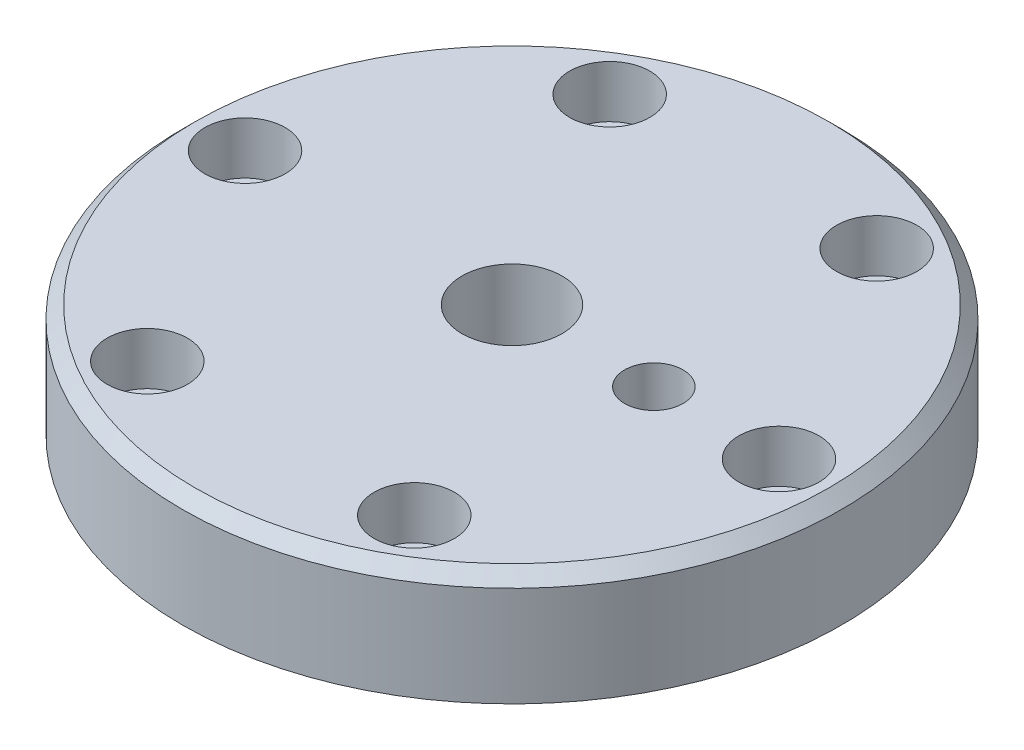
SolidWorks part; units mm, degrees
ref_plane "Front Plane" through (0, 0, 0) normal (0, 0, 1) x (1, 0, 0)
ref_plane "Top Plane" through (0, 0, 0) normal (0, 1, 0) x (1, 0, 0)
ref_plane "Right Plane" through (0, 0, 0) normal (1, 0, 0) x (0, 0, -1)
sketch "Sketch1" plane through (0, 0, 0) normal (0, 1, 0) x (1, 0, 0)
  circle A0 centre (0, 0) radius 79
  circle A1 centre (0, 0) radius 12
extrude "Boss-Extrude1" add sketch "Sketch1" along normal blind 27
hole_wizard "CBORE for M5 Hex Head Bolt1" positions "Sketch2" profile "Sketch3" counterbore size "M5" standard "ANSI Metric" end condition through all
sketch "Sketch2" plane through (0, 27, 0) normal (0, 1, 0) x (1, 0, 0)
  line L0 (0, 0) -> (32, 55.4256) construction
  circle A0 centre (0, 0) radius 64 construction
  point P0 (32, 55.4256)
  point P19 (64, 0)
  point P20 (32, -55.4256)
  point P21 (-32, -55.4256)
  point P22 (-64, 0)
  point P23 (-32, 55.4256)
  point P24 (0, 0)
  dimension "D1" = 6
sketch "Sketch3" plane through (32, 27, -55.4256) normal (1, 0, 0) x (0, 0, 1)
  line L0 (0, 0) -> (0, 27)
  line L1 (0, 27) -> (6.25, 27)
  line L3 (6.25, 27) -> (6.25, 12.5)
  line L4 (6.25, 12.5) -> (9.625, 12.5)
  line L5 (9.625, 12.5) -> (9.625, 0)
  line L7 (9.625, 0) -> (0, 0)
  line L11 (0, -6.35) -> (0, 107.95) construction
  dimension "Thru Hole Dia." = 12.5
  dimension "Thru Hole Depth" = 27
  dimension "C'Bore Dia." = 19.25
  dimension "C'Bore Depth" = 12.5
hole_wizard "Ø1.0mm Dowel Hole1" positions "Sketch6" profile "Sketch7" hole size "Ø1.0" standard "ANSI Metric"
sketch "Sketch6" plane through (0, 27, 0) normal (0, 1, 0) x (1, 0, 0)
  line L0 (-14.85, 0) -> (14.85, 0) construction
  point P0 (34, 0)
  dimension "D1" = 34
sketch "Sketch7" plane through (34, 27, 0) normal (1, 0, 0) x (0, 0, 1)
  line L0 (0, 0) -> (0, 21.206)
  line L1 (0, 21.206) -> (7, 17)
  line L2 (7, 17) -> (7, 0)
  line L5 (7, 0) -> (0, 0)
  line L10 (0, 21.206) -> (-7, 17) construction
  line L11 (0, -6.35) -> (0, 107.95) construction
  dimension "Hole Dia." = 14
  dimension "Hole Depth" = 17
  dimension "Drill Angle" = 118
sketch "Sketch8" plane through (0, 0, 0) normal (0, 1, 0) x (1, 0, 0)
  circle A0 centre (0, 0) radius 22
  circle A1 centre (0, 0) radius 33
  circle A2 centre (0, 0) radius 79 construction
  dimension "D1" = 11
  dimension "D2" = 46
extrude "Cut-Extrude1" cut sketch "Sketch8" along normal blind 6
chamfer "Chamfer1" distance 3 angle 45 1 edges at (0, 27, 79)
